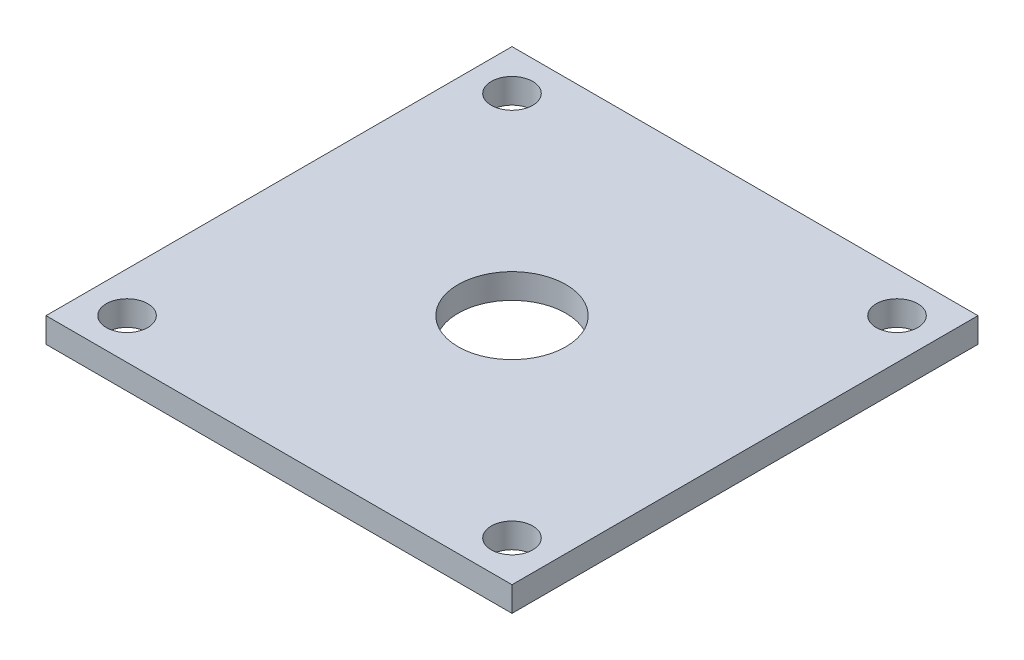
SolidWorks part; units mm, degrees
ref_plane "Front Plane" through (0, 0, 0) normal (0, 0, 1) x (1, 0, 0)
ref_plane "Top Plane" through (0, 0, 0) normal (0, 1, 0) x (1, 0, 0)
ref_plane "Right Plane" through (0, 0, 0) normal (1, 0, 0) x (0, 0, -1)
sketch "Sketch3" plane through (0, 0, 0) normal (0, 1, 0) x (1, 0, 0)
  line L1 (-35.687, 35.687) -> (35.687, 35.687)
  line L2 (-35.687, 35.687) -> (-35.687, -35.687)
  line L3 (-35.687, -35.687) -> (35.687, -35.687)
  line L4 (35.687, 35.687) -> (35.687, -35.687)
  line L5 (-35.687, 35.687) -> (35.687, -35.687) construction
  line L6 (-35.687, -35.687) -> (35.687, 35.687) construction
  point P0 (0, 0)
  dimension "D1" = 71.374
  dimension "D2" = 71.374
extrude "Boss-Extrude1" add sketch "Sketch3" along normal blind 88.9508
shell "Shell1" thickness 5.08
sketch "Sketch4" plane through (0, 83.8708, 0) normal (0, -1, 0) x (-1, 0, 0)
  circle A0 centre (0, 0) radius 8.255
  dimension "D1" = 16.51
extrude "Cut-Extrude1" cut sketch "Sketch4" against normal up to body separate body
sketch "Sketch15" plane through (0, 0, 35.687) normal (0, 0, 1) x (1, 0, 0)
  line L0 (-35.687, 85.1408) -> (35.687, 85.1408)
  line L1 (-35.687, 88.9508) -> (-35.687, 0) construction
  line L2 (35.687, 88.9508) -> (35.687, 0) construction
  line L3 (-35.687, 88.9508) -> (35.687, 88.9508) construction
  line L5 (-35.687, 88.9508) -> (35.687, 88.9508)
  line L6 (-35.687, 88.9508) -> (-35.687, 85.1408)
  line L8 (35.687, 88.9508) -> (35.687, 85.1408)
  dimension "D1" = 3.81
extrude "Cut-Extrude14" cut sketch "Sketch15" against normal through all flip side to cut
sketch "Sketch20" plane through (0, 0, 0) normal (0, 1, 0) x (1, 0, 0)
  line L0 (-35.687, -25.527) -> (-25.527, -35.687) construction
  line L1 (25.527, -35.687) -> (35.687, -25.527) construction
  line L2 (-35.687, 25.527) -> (-25.527, 35.687) construction
  line L3 (25.527, 35.687) -> (35.687, 25.527) construction
  line L4 (-25.527, -25.527) -> (-35.687, -25.527) construction
  line L5 (25.527, -25.527) -> (35.687, -25.527) construction
  line L6 (25.527, 25.527) -> (35.687, 25.527) construction
  line L7 (-25.527, 25.527) -> (-35.687, 25.527) construction
  line L8 (-25.527, 25.527) -> (-25.527, 35.687) construction
  line L9 (25.527, 25.527) -> (25.527, 35.687) construction
  line L10 (25.527, -25.527) -> (25.527, -35.687) construction
  line L11 (-25.527, -25.527) -> (-25.527, -35.687) construction
  line L12 (-29.4825, 29.4825) -> (35.687, 29.4825) construction
  line L13 (35.687, 35.687) -> (35.687, -35.687) construction
  line L14 (-29.4825, 29.4825) -> (-29.4825, -35.687) construction
  line L15 (-35.687, -35.687) -> (35.687, -35.687) construction
  line L16 (29.4848, 29.4848) -> (29.4848, -35.687) construction
  line L17 (-29.4812, -29.4812) -> (35.687, -29.4812) construction
  circle A0 centre (-29.4825, 29.4825) radius 3.175
  circle A1 centre (29.4848, -29.4848) radius 3.175
  circle A2 centre (-29.4812, -29.4812) radius 3.175
  circle A3 centre (29.4848, 29.4848) radius 3.175
extrude "Cut-Extrude15" cut sketch "Sketch20" against normal through all from surface at 88.9508 starting at face at (0, 88.9508, 8.255)
sketch "Sketch6" plane through (0, 0, 30.607) normal (0, 0, -1) x (-1, 0, 0)
  line L0 (30.607, 5.08) -> (-30.607, 5.08) construction
  line L1 (30.607, 83.8708) -> (30.607, 5.08) construction
  line L2 (-30.607, 83.8708) -> (-30.607, 5.08) construction
  line L3 (30.607, 2.54) -> (-30.607, 2.54) construction
  line L4 (35.687, 83.8708) -> (35.687, 0) construction
  line L5 (30.607, 83.8708) -> (-30.607, 83.8708) construction
  line L6 (30.607, 0) -> (-30.607, 0) construction
  line L7 (37.0041, 83.8708) -> (37.0041, 94.0309) construction
  line L8 (-35.687, 83.8708) -> (-35.687, 0) construction
  line L10 (35.687, 5.08) -> (-35.687, 5.08)
  line L11 (35.687, 5.08) -> (35.687, 0)
  line L12 (35.687, 0) -> (-35.687, 0)
  line L13 (-35.687, 5.08) -> (-35.687, 0)
  dimension "D1" = 2.54
  dimension "D2" = 2.54
  dimension "D3" = 5.08
  dimension "D4" = 5.08
extrude "Cut-Extrude3" cut sketch "Sketch6" against normal up to body separate body
sketch "Sketch7" plane through (-35.687, 0, 0) normal (-1, 0, 0) x (0, 0, 1)
  line L0 (30.607, 2.54) -> (-30.607, 2.54) construction
  line L1 (30.607, 83.8708) -> (30.607, 5.08) construction
  line L2 (-30.607, 83.8708) -> (-30.607, 5.08) construction
  line L3 (30.607, 0) -> (-30.607, 0) construction
  line L4 (30.607, 5.08) -> (-30.607, 5.08) construction
  line L5 (-66.294, 83.8708) -> (-66.294, 0) construction
  line L6 (30.607, 83.8708) -> (-30.607, 83.8708) construction
  dimension "D1" = 2.54
  dimension "D2" = 5.08
  dimension "D3" = 35.687
equation "\"2.81inch\"=62.2233"
equation "\"3.502inch\"=10"
